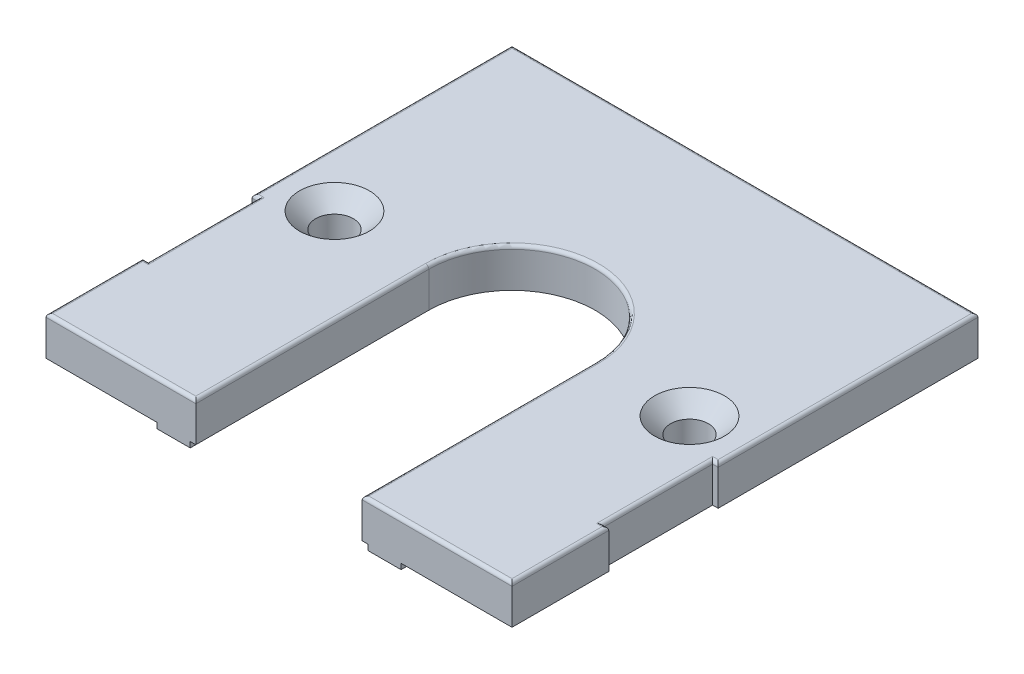
SolidWorks part; units mm, degrees
ref_plane "Alzado" through (0, 0, 0) normal (0, 0, 1) x (1, 0, 0)
ref_plane "Planta" through (0, 0, 0) normal (0, 1, 0) x (1, 0, 0)
ref_plane "Vista lateral" through (0, 0, 0) normal (1, 0, 0) x (0, 0, -1)
sketch "Croquis1" plane through (0, 0, 0) normal (0, 1, 0) x (1, 0, 0)
  line L0 (-7.5, 0) -> (-7.5, -21)
  line L1 (-21, 21) -> (21, 21)
  line L2 (-21, 21) -> (-21, -2.42)
  line L3 (-21, -21) -> (-7.5, -21)
  line L4 (21, 21) -> (21, -2.42)
  line L5 (-21, 21) -> (21, -21) construction
  line L6 (-21, -21) -> (21, 21) construction
  line L7 (7.5, 0) -> (7.5, -21)
  line L8 (7.5, -21) -> (21, -21)
  line L9 (-28.8219, 0) -> (24.5709, 0) construction
  line L10 (-16, 21) -> (-16, -21) construction
  line L11 (16, 21) -> (16, -21) construction
  line L12 (-21, -12.28) -> (-20.5, -12.28)
  line L13 (21, -12.28) -> (21, -21)
  line L14 (20.5, -2.42) -> (20.5, -12.28)
  line L15 (20.5, -2.42) -> (21, -2.42)
  line L16 (-21, -2.42) -> (-20.5, -2.42)
  line L18 (-20.5, -2.42) -> (-20.5, -12.28)
  line L19 (-21, -12.28) -> (-21, -21)
  line L20 (20.5, -12.28) -> (21, -12.28)
  line L21 (-21, -2.42) -> (-7.5, -2.42) construction
  line L22 (21, 21) -> (21, -21) construction
  line L23 (-21, -12.28) -> (-7.5, -12.28) construction
  line L24 (-21, 21) -> (-21, -21) construction
  arc A0 (7.5, 0) -> (-7.5, 0) centre (0, 0) ccw
  point P0 (0, 0)
  point P19 (7.5, -13)
  point P21 (-20, 21)
  point P22 (-20, -21)
  point P23 (20, 21)
  point P24 (20, -21)
  point P27 (7.5, -2)
  dimension "D3" = 15
  dimension "D1" = 42
  dimension "D2" = 42
  dimension "D7" = 0.5
  dimension "D8" = 0.5
  dimension "D9" = 8.72
  dimension "D11" = 9.86
  dimension "D4" = 5
  dimension "D5" = 5
  dimension "D6" = 8.72
  dimension "D10" = 9.86
extrude "Saliente-Extruir1" add sketch "Croquis1" against normal blind 3.5
hole_wizard "Avellanado para tornillo con cabeza plana avellanada de M31" positions "Croquis3" profile "Croquis2" countersink size "M3" standard "ISO" end condition through all
sketch "Croquis3" plane through (0, 0, 0) normal (0, 1, 0) x (1, 0, 0)
  line L0 (-16, 21) -> (-16, -21) construction
  line L1 (16, 21) -> (16, -21) construction
  point P2 (-16, 0)
  point P6 (16, 0)
sketch "Croquis2" plane through (-16, 0, 0) normal (1, 0, 0) x (0, 0, 1)
  line L0 (0, 0) -> (0, 3.5)
  line L1 (0, 3.5) -> (1.7, 3.5)
  line L2 (1.7, 3.5) -> (1.7, 1.45)
  line L3 (1.7, 1.45) -> (3.15, 0)
  line L5 (3.15, 0) -> (0, 0)
  line L6 (-1.7, 1.45) -> (-3.15, 0) construction
  line L11 (0, -6.35) -> (0, 107.95) construction
  dimension "Diámetro de taladro hasta el siguiente" = 3.4
  dimension "Profundidad de taladro hasta el siguiente" = 3.5
  dimension "Diámetro de avellanado cercano" = 6.3
  dimension "Ángulo de avellanado cercano" = 90
fillet "Redondeo1" radius 0.3 16 edges at (-7.5, 0, 10.5) (0, 0, -7.5) (-21, 0, -9.29) (-20.75, 0, 2.42) (-20.5, 0, 7.35) (-20.75, 0, 12.28) (-21, 0, 16.64) (-14.25, 0, 21) (7.5, 0, 10.5) (14.25, 0, 21) (21, 0, 16.64) (20.75, 0, 12.28) (20.5, 0, 7.35) (20.75, 0, 2.42) (21, 0, -9.29) (0, 0, -21)
sketch "Croquis4" plane through (0, -3.5, 0) normal (0, -1, 0) x (1, 0, 0)
  line L2 (11, -21) -> (11, 21)
  line L3 (-11, 21) -> (-11, -21)
  line L4 (21, -21) -> (-21, -21) construction
  line L5 (7.5, 21) -> (21, 21) construction
  line L6 (-21, 21) -> (-7.5, 21) construction
  line L7 (11, -21) -> (8, -21)
  line L8 (8, 21) -> (11, 21)
  line L9 (-11, 21) -> (-8, 21)
  line L10 (8, -21) -> (8, 21)
  line L11 (-8, 21) -> (-8, -21)
  line L12 (-8, -21) -> (-11, -21)
  dimension "D1" = 3
extrude "Saliente-Extruir2" add sketch "Croquis4" along normal blind 0.5
sketch "Croquis5" plane through (0, -3.5, 0) normal (0, -1, 0) x (1, 0, 0)
  line L0 (-22.213, -7.7) -> (25.2444, -7.7) construction
  line L1 (-22.213, -11.2) -> (25.2444, -11.2) construction
  line L2 (0, -21) -> (0, 8.6418) construction
  line L3 (8, -21) -> (-8, -21) construction
  line L4 (-5.5, -11.2) -> (5.5, -11.2) construction
  line L5 (-5.5, -9.7) -> (5.5, -9.7)
  line L6 (-5.5, -12.7) -> (5.5, -12.7)
  line L7 (-11, -21) -> (-21, -21) construction
  arc A0 (-5.5, -9.7) -> (-5.5, -12.7) centre (-5.5, -11.2) ccw
  arc A1 (5.5, -12.7) -> (5.5, -9.7) centre (5.5, -11.2) ccw
  point P10 (0, -11.2)
  dimension "D2" = 9.8
  dimension "D1" = 3.5
extrude "Cortar-Extruir1" cut sketch "Croquis5" against normal blind 2
